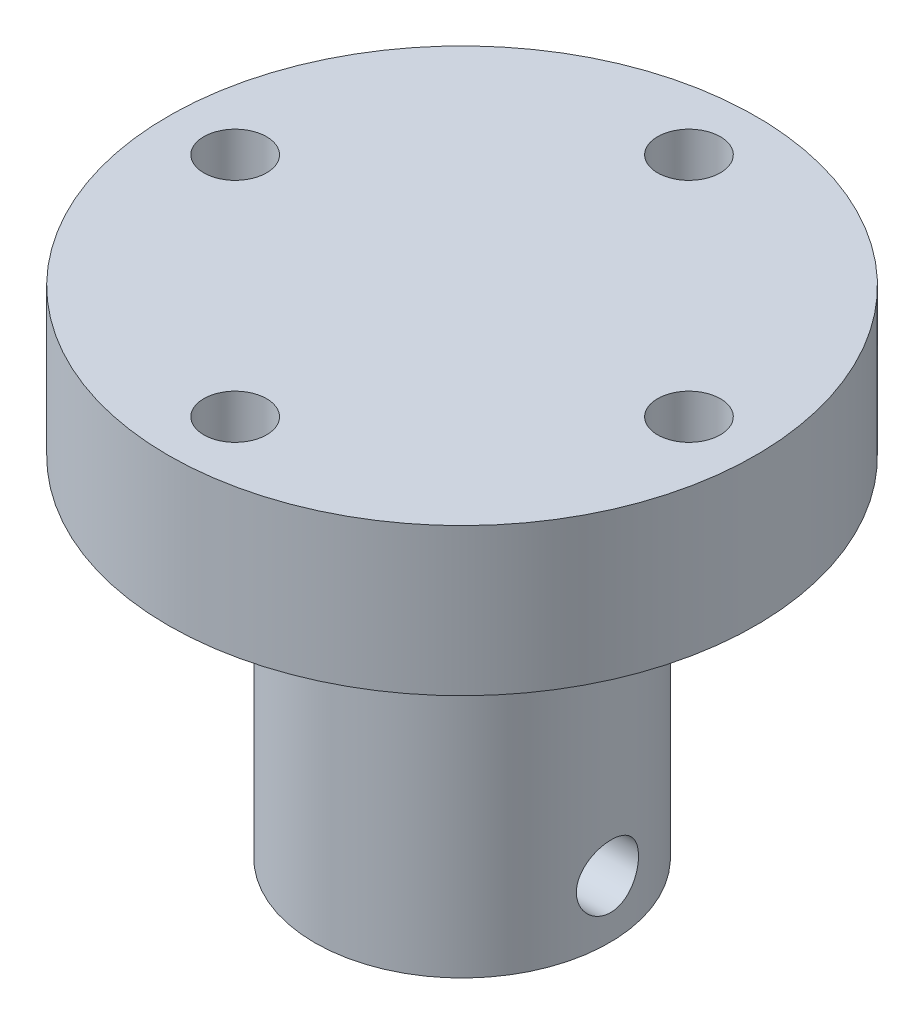
SolidWorks part; units mm, degrees
ref_plane "Front Plane" through (0, 0, 0) normal (0, 0, 1) x (1, 0, 0)
ref_plane "Top Plane" through (0, 0, 0) normal (0, 1, 0) x (1, 0, 0)
ref_plane "Right Plane" through (0, 0, 0) normal (1, 0, 0) x (0, 0, -1)
sketch "Sketch1" plane through (0, 0, 0) normal (0, -1, 0) x (0, 0, -1)
  circle A0 centre (0, 0) radius 6.35
  dimension "D1" = 12.7
extrude "Boss-Extrude1" add sketch "Sketch1" along normal blind 15
sketch "Sketch2" plane through (0, 0, 0) normal (0, 1, 0) x (1, 0, 0)
  circle A0 centre (0, 0) radius 3.1
  dimension "D1" = 6.2
extrude "Cut-Extrude1" cut sketch "Sketch2" against normal blind 10
sketch "Sketch3" plane through (0, -15, 0) normal (0, -1, 0) x (1, 0, 0)
  circle A0 centre (0, 0) radius 4.1
  dimension "D1" = 8.2
extrude "Cut-Extrude2" cut sketch "Sketch3" against normal blind 5
sketch "Sketch11" plane through (0, 0, 0) normal (1, 0, 0) x (0, 0, -1)
  line L0 (0, 0) -> (0, -14.8732) construction
hole_wizard "#6-32 Tapped Hole1" positions "3DSketch5" profile "Sketch12" tap size "#6-32" standard "ANSI Inch"
sketch3d "3DSketch5"
  line L0 (0, 0, 0) -> (0, -14.8732, 0) construction
  point P0 (0, -5, 0)
  point P7 (0, -2.9681, 0)
  point P9 (-6.3497, -3.6851, 0.0615)
  dimension "D1" = 5
sketch "Sketch12" plane through (-6.3497, -3.6851, 0.0615) normal (0, 1, 0) x (0.0097, 0, 1)
  line L0 (0, 0) -> (0, 7.8127)
  line L1 (0, 7.8127) -> (1.3525, 7)
  line L2 (1.3525, 7) -> (1.3525, 0)
  line L5 (1.3525, 0) -> (0, 0)
  line L10 (0, 7.8127) -> (-1.3526, 7) construction
  line L11 (0, -6.35) -> (0, 107.95) construction
  dimension "Tap Drill Dia." = 2.7051
  dimension "Tap Drill Depth" = 7
  dimension "Drill Angle" = 118
cosmetic thread "Hole Thread6" parameters "D1"=3.5606, "D2"=3.5052
hole_wizard "#6-32 Tapped Hole2" positions "3DSketch6" profile "Sketch13" tap size "#6-32" standard "ANSI Inch" end condition through all
sketch3d "3DSketch6"
  point P0 (-6.3497, -12.5453, 0.0629)
sketch "Sketch13" plane through (-6.3497, -12.5453, 0.0629) normal (0, 1, 0) x (0.0099, 0, 1)
  line L0 (0, 0) -> (0, 12.7626)
  line L1 (0, 12.7626) -> (1.3525, 12.7626)
  line L2 (1.3525, 12.7626) -> (1.3525, 0)
  line L5 (1.3525, 0) -> (0, 0)
  line L11 (0, -6.35) -> (0, 107.95) construction
  dimension "Thru Tap Drill Dia." = 2.7051
  dimension "Thru Tap Drill Depth" = 12.7626
cosmetic thread "Hole Thread7" parameters "D2"=3.5052
sketch "Sketch14" plane through (0, 0, 0) normal (0, 1, 0) x (1, 0, 0)
  circle A0 centre (0, 0) radius 12.661
  dimension "D1" = 25.3219
extrude "Boss-Extrude2" add sketch "Sketch14" along normal blind 6.35
sketch "Sketch16" plane through (0, 0, 0) normal (0, 1, 0) x (1, 0, 0)
  circle A0 centre (0, 0) radius 9.779 construction
  dimension "D1" = 19.558
hole_wizard "#6-32 Tapped Hole3" positions "Sketch17" profile "Sketch18" tap size "#6-32" standard "ANSI Inch" end condition through all
sketch "Sketch17" plane through (0, 0, 0) normal (0, -1, 0) x (-1, 0, 0)
  circle A0 centre (0, 0) radius 9.779 construction
  point P0 (-9.779, 0)
  point P4 (0, 9.779)
  point P6 (9.779, 0)
  point P8 (0, -9.779)
sketch "Sketch18" plane through (9.779, 0, 0) normal (1, 0, 0) x (0, 0, -1)
  line L0 (0, 0) -> (0, 6.35)
  line L1 (0, 6.35) -> (1.3525, 6.35)
  line L2 (1.3525, 6.35) -> (1.3525, 0)
  line L5 (1.3525, 0) -> (0, 0)
  line L11 (0, -6.35) -> (0, 107.95) construction
  dimension "Thru Tap Drill Dia." = 2.7051
  dimension "Thru Tap Drill Depth" = 6.35
cosmetic thread "Hole Thread8" parameters "D2"=3.5052
cosmetic thread "Hole Thread9" parameters "D2"=3.5052
cosmetic thread "Hole Thread10" parameters "D2"=3.5052
cosmetic thread "Hole Thread11" parameters "D2"=3.5052
